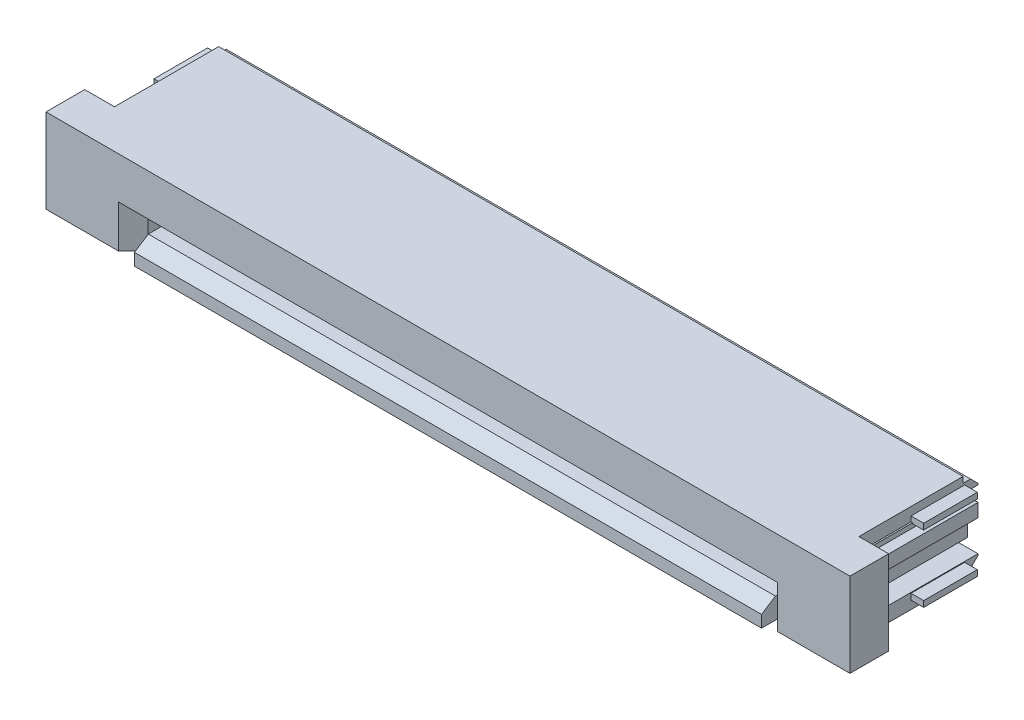
SolidWorks part; units mm, degrees
material "policarbonato"
ref_plane "Front" through (0, 0, 0) normal (0, 0, 1) x (1, 0, 0)
ref_plane "Top" through (0, 0, 0) normal (0, 1, 0) x (1, 0, 0)
ref_plane "Side" through (0, 0, 0) normal (1, 0, 0) x (0, 0, -1)
sketch "Sketch1" plane through (0, 0, 0) normal (1, 0, 0) x (0, 0, -1)
  line L0 (-1.75, 1.5) -> (1.75, 1.5)
  line L1 (2, 1.3) -> (1.75, 1.3)
  line L2 (1.75, 1.5) -> (1.75, 1.3)
  line L3 (2.25, 1.05) -> (2, 1.3)
  line L4 (2.25, -1.05) -> (2.25, 1.05)
  line L5 (2, -1.3) -> (2.25, -1.05)
  line L6 (1.75, -1.3) -> (1.75, -1.5)
  line L7 (2, -1.3) -> (1.75, -1.3)
  line L8 (-3.05, -1.5) -> (1.75, -1.5)
  line L9 (-1.75, -0.65) -> (-1.75, 1.5)
  line L10 (-2.35, -0.65) -> (-1.75, -0.65)
  line L11 (-2.35, -0.65) -> (-3.05, -1.1)
  line L12 (-3.05, -1.5) -> (-3.05, -1.1)
  line L13 (-1.75, 1.5) -> (1.75, -1.5) construction
  point P1 (0, 0)
  dimension "D1" = 45
  dimension "D2" = 45
  dimension "D3" = 3.5
  dimension "D4" = 0.25
  dimension "D5" = 0.5
  dimension "D6" = 0.2
  dimension "D7" = 1.3
  dimension "D8" = 32.735
  dimension "D9" = 0.6
  dimension "D10" = 3
  dimension "D11" = 0.4
  dimension "D12" = 0.2
extrude "Base" add sketch "Sketch1" along normal mid plane 25
sketch "Sketch2" plane through (0, 0, 3.05) normal (0, 0, 1) x (1, 0, 0)
  line L0 (12.5, -1.5) -> (-12.5, -1.5) construction
  line L1 (-10.6, 0.75) -> (10.6, 0.75)
  line L2 (-10.6, 0.75) -> (-10.6, -0.8)
  line L3 (-10.6, -0.8) -> (10.6, -0.8)
  line L4 (10.6, 0.75) -> (10.6, -0.8)
  line L5 (12.5, 1.5) -> (-12.5, 1.5) construction
  line L6 (-12.5, 1.5) -> (-12.5, -0.65) construction
  line L7 (12.5, 1.5) -> (12.5, -0.65) construction
  dimension "D1" = 0.7
  dimension "D2" = 0.75
  dimension "D3" = 1.9
  dimension "D4" = 1.9
extrude "Card Slot" cut sketch "Sketch2" against normal blind 3.8
sketch "Sketch4" plane through (0, 0, 1.75) normal (0, 0, 1) x (1, 0, 0)
  line L0 (12.5, 1.5) -> (12.5, -0.65) construction
  line L1 (-12.5, 1) -> (-10.725, 1)
  line L2 (-12.5, 1) -> (-12.5, -1)
  line L3 (-12.5, -1) -> (-10.725, -1)
  line L4 (-10.725, 1) -> (-10.725, -1)
  line L5 (12.5, 1) -> (10.725, 1)
  line L6 (12.5, 1) -> (12.5, -1)
  line L7 (12.5, -1) -> (10.725, -1)
  line L8 (10.725, 1) -> (10.725, -1)
  line L9 (12.5, -1.5) -> (-12.5, -1.5) construction
  line L11 (12.5, 1.5) -> (-12.5, 1.5) construction
  line L12 (-12.5, 1.5) -> (-12.5, -0.65) construction
  dimension "D1" = 0.5
  dimension "D2" = 0.5
  dimension "D3" = 1.775
extrude "Wings" cut sketch "Sketch4" against normal through all
sketch "Sketch5" plane through (0, 0, 3.05) normal (0, 0, 1) x (1, 0, 0)
  line L0 (12.5, -1.5) -> (-12.5, -1.5) construction
  line L1 (-12.5, 1.5) -> (-10.53, 1.5)
  line L2 (-12.5, 1.5) -> (-12.5, -1.5)
  line L3 (-12.5, -1.5) -> (-10.53, -1.5)
  line L4 (-10.53, 1.5) -> (-10.53, -1.5)
  line L5 (0, 0) -> (0, 2.0181) construction
  line L6 (12.5, 1.5) -> (10.53, 1.5)
  line L7 (12.5, 1.5) -> (12.5, -1.5)
  line L8 (12.5, -1.5) -> (10.53, -1.5)
  line L9 (10.53, 1.5) -> (10.53, -1.5)
  dimension "D1" = 1.97
extrude "Front Lead In" cut sketch "Sketch5" against normal up to surface (1.3 mm away) up to face at (0, 0.4917, 1.75)
chamfer "Card Slot Lead In" distance 0.1 angle 60 3 edges at (10.6, -0.025, 1.75) (0, 0.75, 1.75) (-10.6, -0.025, 1.75)
ref_plane "POS 1 Plane" through (9.5, 0, 0) normal (1, 0, 0) x (0, 0, -1)
ref_plane "WT Plane" through (0, 0, 0) normal (0, 0, 1) x (1, 0, 0)
sketch "Sketch8" plane through (0, 0, 0) normal (0, 0, 1) x (1, 0, 0)
  line L0 (0, 0) -> (0, 411) construction
  line L1 (-12.5, -1) -> (-12.5, -1.5) construction
  line L4 (12.5, -1.5) -> (12.5, -1.3) construction
  line L5 (12.5, 1.5) -> (-12.5, 1.5) construction
  point P8 (12.5, -1.4)
  line B0 (-12.925, 1.025) -> (-11.075, 1.025)
  line B1 (-11.075, 1.225) -> (-12.925, 1.225)
  line B2 (-12.925, 1.025) -> (-12.925, 1.225)
  line B3 (-10.725, -0.875) -> (-10.725, 0.875)
  line B4 (-10.925, 0.875) -> (-10.925, -0.875)
  line B5 (-11.075, -1.025) -> (-12.925, -1.025)
  line B6 (-12.925, -1.225) -> (-12.925, -1.025)
  line B7 (-12.925, -1.225) -> (-11.075, -1.225)
  arc B8 (-10.725, 0.875) -> (-11.075, 1.225) centre (-11.075, 0.875) ccw
  arc B9 (-10.925, 0.875) -> (-11.075, 1.025) centre (-11.075, 0.875) ccw
  arc B10 (-11.075, -1.225) -> (-10.725, -0.875) centre (-11.075, -0.875) ccw
  arc B11 (-11.075, -1.025) -> (-10.925, -0.875) centre (-11.075, -0.875) ccw
  line B12 (12.925, 1.025) -> (11.075, 1.025)
  line B13 (11.075, 1.225) -> (12.925, 1.225)
  line B14 (12.925, 1.025) -> (12.925, 1.225)
  line B15 (10.725, -0.875) -> (10.725, 0.875)
  line B16 (10.925, 0.875) -> (10.925, -0.875)
  line B17 (11.075, -1.025) -> (12.925, -1.025)
  line B18 (12.925, -1.225) -> (12.925, -1.025)
  line B19 (12.925, -1.225) -> (11.075, -1.225)
  arc B20 (10.725, 0.875) -> (11.075, 1.225) centre (11.075, 0.875) cw
  arc B21 (10.925, 0.875) -> (11.075, 1.025) centre (11.075, 0.875) cw
  arc B22 (11.075, -1.225) -> (10.725, -0.875) centre (11.075, -0.875) cw
  arc B23 (11.075, -1.025) -> (10.925, -0.875) centre (11.075, -0.875) cw
  dimension "D1" = 0.425
  dimension "D2" = 0.425
  dimension "D3" = 0.275
sketch_block_instance "Block2-1"
sketch_block "Block2"
sketch_block_instance "Block2-3"
extrude "WT" add sketch "Sketch8" against normal blind 1.8
sketch "Sketch9" plane through (0, 0, 1.75) normal (0, 0, 1) x (1, 0, 0)
  line L1 (-12.5, -1.5) -> (-10.53, -1.5) construction
  line L2 (10.57, 0.1) -> (10.57, -1.33)
  line L3 (-10.57, 0.1) -> (10.57, 0.1)
  line L4 (10.57, -1.33) -> (13.5, -1.33)
  line L5 (13.5, -1.33) -> (13.5, 1.5)
  line L6 (13.5, 1.5) -> (-13.5, 1.5)
  line L7 (-13.5, 1.5) -> (-13.5, -1.33)
  line L8 (-13.5, -1.33) -> (-10.57, -1.33)
  line L9 (-10.57, -1.33) -> (-10.57, 0.1)
  line L10 (-12.925, 1.225) -> (-12.925, 1.025) construction
  point P2 (0, 0.1)
  dimension "D1" = 0.1
  dimension "D2" = 2.83
  dimension "D3" = 2.93
  dimension "D4" = 0.575
  dimension "D5" = 0.17
extrude "Gate" add sketch "Sketch9" along normal blind 1.3
chamfer "Gate Chamfer" distance 0.5 angle 45 2 edges at (10.57, -0.615, 3.05) (-10.57, -0.615, 3.05)
sketch "Sketch10" plane through (0, 0, 1.75) normal (0, 0, -1) x (-1, 0, 0)
  line L0 (-13.5, -1.33) -> (-13.5, 1.5) construction
  line L1 (-12.55, -0.3) -> (-12.55, 0.4451)
  line L2 (-12, -0.3) -> (-12.55, -0.3)
  line L3 (-13.5, 1.5) -> (-12.5, 1.5) construction
  line L4 (11.625, -0.2019) -> (11.625, 0.3755)
  line L5 (0, 0) -> (0, 3.8889) construction
  line L6 (-11.9, 0.3755) -> (-11.625, 0.3755)
  line L7 (-11.9, 0.3755) -> (-11.9, 1.05)
  line L8 (-11.9, 1.05) -> (-12.55, 1.05)
  line L9 (-12.55, 1.05) -> (-12.55, 0.8951)
  line L10 (-12.55, 0.8951) -> (-12.9, 0.8951)
  line L11 (-12.9, 0.8951) -> (-12.9, 0.4451)
  line L12 (-12.9, 0.4451) -> (-12.55, 0.4451)
  line L13 (12, -0.2019) -> (11.625, -0.2019)
  line L14 (-12, -0.3) -> (-12, -0.2019)
  line L15 (-12, -0.2019) -> (-11.625, -0.2019)
  line L16 (12, -0.3) -> (12, -0.2019)
  line L17 (-11.625, -0.2019) -> (-11.625, 0.3755)
  line L18 (12.9, 0.4451) -> (12.55, 0.4451)
  line L19 (12.9, 0.8951) -> (12.9, 0.4451)
  line L20 (12.55, 0.8951) -> (12.9, 0.8951)
  line L21 (12.55, 1.05) -> (12.55, 0.8951)
  line L22 (11.9, 1.05) -> (12.55, 1.05)
  line L23 (11.9, 0.3755) -> (11.9, 1.05)
  line L24 (11.9, 0.3755) -> (11.625, 0.3755)
  line L25 (12, -0.3) -> (12.55, -0.3)
  line L26 (12.55, -0.3) -> (12.55, 0.4451)
  dimension "D1" = 1.35
  dimension "D2" = 0.65
  dimension "D3" = 0.35
  dimension "D4" = 0.45
  dimension "D5" = 0.35
  dimension "D6" = 0.7451
  dimension "D7" = 0.55
  dimension "D8" = 0.0981
  dimension "D9" = 0.375
  dimension "D10" = 0.6
  dimension "D11" = 0.45
  dimension "D12" = 0.275
  dimension "D13" = 0.6745
extrude "Gate Guide" add sketch "Sketch10" along normal blind 3.6
sketch "Sketch6" plane through (9.5, 0, 0) normal (1, 0, 0) x (0, 0, -1)
  line L0 (-1.75, -1.5) -> (1.75, -1.5) construction
  line L3 (0.75, 0.75) -> (0.75, -0.8) construction
  line B0 (1.8966, 1.1164) -> (1.8966, 1.1134)
  line B1 (1.1383, -0.6804) -> (-1.1565, -0.4395)
  line B2 (1.1383, -0.6804) -> (1.5518, -0.6804)
  line B3 (1.8966, -0.6772) -> (1.8966, -0.6743)
  line B4 (2.2503, -0.3242) -> (2.2503, -0.6772)
  line B5 (2.2503, 0.5618) -> (2.2503, -0.1226)
  line B6 (3.7503, 1.3984) -> (3.7503, 1.3222)
  line B7 (2.5059, 0.815) -> (2.3646, 0.815)
  line B8 (3.069, 1.176) -> (2.7405, 0.9004)
  line B9 (3.6487, 1.2206) -> (3.1915, 1.2206)
  line B10 (3.1915, 1.5) -> (3.6487, 1.5)
  line B11 (2.6097, 1.1553) -> (2.8894, 1.3901)
  line B12 (1.5518, 1.1196) -> (-1.3757, 1.1196)
  line B13 (-1.0668, 0.7796) -> (-1.4132, 0.9796)
  line B14 (1.3415, 0.5196) -> (1.3415, 0.449)
  line B15 (1.0915, 0.7696) -> (-1.0293, 0.7696)
  line B16 (-1.1045, -0.2363) -> (0.5626, -0.3004)
  line B17 (-1.6498, -0.425) -> (-1.3625, -0.0694)
  arc B18 (1.6915, -0.5407) -> (1.5518, -0.6804) centre (1.5518, -0.5407) cw
  arc B19 (1.6915, -0.5407) -> (1.8966, -0.6743) centre (1.7506, -0.6743) cw
  arc B20 (2.2503, -0.6772) -> (1.8966, -0.6772) centre (2.0735, -0.6772) cw
  arc B21 (2.2503, -0.3242) -> (2.2503, -0.1226) centre (2.3646, -0.2234) cw
  arc B22 (3.6487, 1.5) -> (3.7503, 1.3984) centre (3.6487, 1.3984) cw
  arc B23 (3.7503, 1.3222) -> (3.6487, 1.2206) centre (3.6487, 1.3222) cw
  arc B24 (2.2503, 0.5618) -> (2.3646, 0.815) centre (2.3646, 0.6626) cw
  arc B25 (2.7405, 0.9004) -> (2.5059, 0.815) centre (2.5059, 1.18) cw
  arc B26 (3.069, 1.176) -> (3.1915, 1.2206) centre (3.1915, 1.0301) cw
  arc B27 (2.8894, 1.3901) -> (3.1915, 1.5) centre (3.1915, 1.0301) cw
  arc B28 (2.6097, 1.1553) -> (2.2216, 1.213) centre (2.4412, 1.3561) cw
  arc B29 (1.8966, 1.1164) -> (2.2216, 1.213) centre (2.0735, 1.1164) cw
  arc B30 (1.8966, 1.1134) -> (1.6915, 0.9799) centre (1.7506, 1.1134) cw
  arc B31 (1.5518, 1.1196) -> (1.6915, 0.9799) centre (1.5518, 0.9799) cw
  arc B32 (-1.4132, 0.9796) -> (-1.3757, 1.1196) centre (-1.3757, 1.0446) cw
  arc B33 (-1.0293, 0.7696) -> (-1.0668, 0.7796) centre (-1.0293, 0.8446) cw
  arc B34 (1.0915, 0.7696) -> (1.3415, 0.5196) centre (1.0915, 0.5196) cw
  arc B35 (1.3415, 0.449) -> (0.5626, -0.3004) centre (0.5915, 0.449) cw
  arc B36 (-1.1045, -0.2363) -> (-1.25, -0.1019) centre (-1.0986, -0.084) cw
  arc B37 (-1.3625, -0.0694) -> (-1.25, -0.1019) centre (-1.3131, -0.1093) cw
  arc B38 (-1.5704, -0.5208) -> (-1.6498, -0.425) centre (-1.6004, -0.4649) cw
  arc B39 (-1.5704, -0.5208) -> (-1.1565, -0.4395) centre (-1.2313, -1.1525) cw
  dimension "D1" = 3
  dimension "D2" = 2
sketch_block_instance "Block4-1"
sketch_block "Block4"
sketch "Sketch13" plane through (9.5, 0, 0) normal (1, 0, 0) x (0, 0, -1)
  line L0 (1.75, 1.5) -> (-1.75, 1.5) construction
  line L1 (0.75, -0.8) -> (0.75, 0.75) construction
  arc B0 (1.0915, -0.7696) -> (1.3415, -0.5196) centre (1.0915, -0.5196) ccw
  line B1 (1.0915, -0.7696) -> (-1.0293, -0.7696)
  line B2 (1.5518, -1.1196) -> (-1.3757, -1.1196)
  line B3 (2.2503, 0.6075) -> (-5.2255, 0.6075) construction
  line B4 (-1.6498, 0.425) -> (-1.3625, 0.0694)
  line B5 (-1.1045, 0.2363) -> (0.5626, 0.3004)
  line B6 (1.3415, -0.5196) -> (1.3415, -0.449)
  line B7 (-1.0668, -0.7796) -> (-1.4132, -0.9796)
  line B8 (2.6097, -1.1553) -> (2.8894, -1.3901)
  line B9 (3.1915, -1.5) -> (3.6487, -1.5)
  line B10 (3.6487, -1.2206) -> (3.1915, -1.2206)
  line B11 (3.069, -1.176) -> (2.7405, -0.9004)
  line B12 (2.5059, -0.815) -> (2.3646, -0.815)
  line B13 (3.7503, -1.3984) -> (3.7503, -1.3222)
  line B14 (2.2503, -0.5618) -> (2.2503, 0.1226)
  line B15 (2.2503, 0.3242) -> (2.2503, 0.6772)
  line B16 (1.8966, 0.6772) -> (1.8966, 0.6742)
  line B17 (1.1383, 0.6804) -> (1.5518, 0.6804)
  line B18 (1.1383, 0.6804) -> (-1.1565, 0.4395)
  line B19 (1.8966, -1.1135) -> (1.8966, -1.1164)
  arc B20 (-1.5704, 0.5208) -> (-1.1565, 0.4395) centre (-1.2313, 1.1525) ccw
  arc B21 (-1.5704, 0.5208) -> (-1.6498, 0.425) centre (-1.6004, 0.4649) ccw
  arc B22 (-1.3625, 0.0694) -> (-1.25, 0.1019) centre (-1.3131, 0.1093) ccw
  arc B23 (-1.1045, 0.2363) -> (-1.25, 0.1019) centre (-1.0986, 0.084) ccw
  arc B24 (1.3415, -0.449) -> (0.5626, 0.3004) centre (0.5915, -0.449) ccw
  arc B25 (-1.0293, -0.7696) -> (-1.0668, -0.7796) centre (-1.0293, -0.8446) ccw
  arc B26 (-1.4132, -0.9796) -> (-1.3757, -1.1196) centre (-1.3757, -1.0446) ccw
  arc B27 (1.5518, -1.1196) -> (1.6915, -0.9799) centre (1.5518, -0.9799) ccw
  arc B28 (1.8966, -1.1135) -> (1.6915, -0.9799) centre (1.7506, -1.1135) ccw
  arc B29 (1.8966, -1.1164) -> (2.2216, -1.213) centre (2.0735, -1.1164) ccw
  arc B30 (2.6097, -1.1553) -> (2.2216, -1.213) centre (2.4412, -1.3561) ccw
  arc B31 (2.8894, -1.3901) -> (3.1915, -1.5) centre (3.1915, -1.0301) ccw
  arc B32 (3.069, -1.176) -> (3.1915, -1.2206) centre (3.1915, -1.0301) ccw
  arc B33 (2.7405, -0.9004) -> (2.5059, -0.815) centre (2.5059, -1.18) ccw
  arc B34 (2.2503, -0.5618) -> (2.3646, -0.815) centre (2.3646, -0.6626) ccw
  arc B35 (3.7503, -1.3222) -> (3.6487, -1.2206) centre (3.6487, -1.3222) ccw
  arc B36 (3.6487, -1.5) -> (3.7503, -1.3984) centre (3.6487, -1.3984) ccw
  arc B37 (2.2503, 0.3242) -> (2.2503, 0.1226) centre (2.3646, 0.2234) ccw
  arc B38 (2.2503, 0.6772) -> (1.8966, 0.6772) centre (2.0735, 0.6772) ccw
  arc B39 (1.6915, 0.5407) -> (1.8966, 0.6742) centre (1.7506, 0.6742) ccw
  arc B40 (1.6915, 0.5407) -> (1.5518, 0.6804) centre (1.5518, 0.5407) ccw
  dimension "D1" = 3
  dimension "D2" = 2
sketch_block_instance "Block1-5"
sketch_block "Block1" parameters "D1"=5.4663
extrude "-01 Contact" add sketch "Sketch13" along normal mid plane 0.25
pattern_linear "LPattern3" count 20 spacing 1 along (-1, 0, 0) of "-01 Contact"
